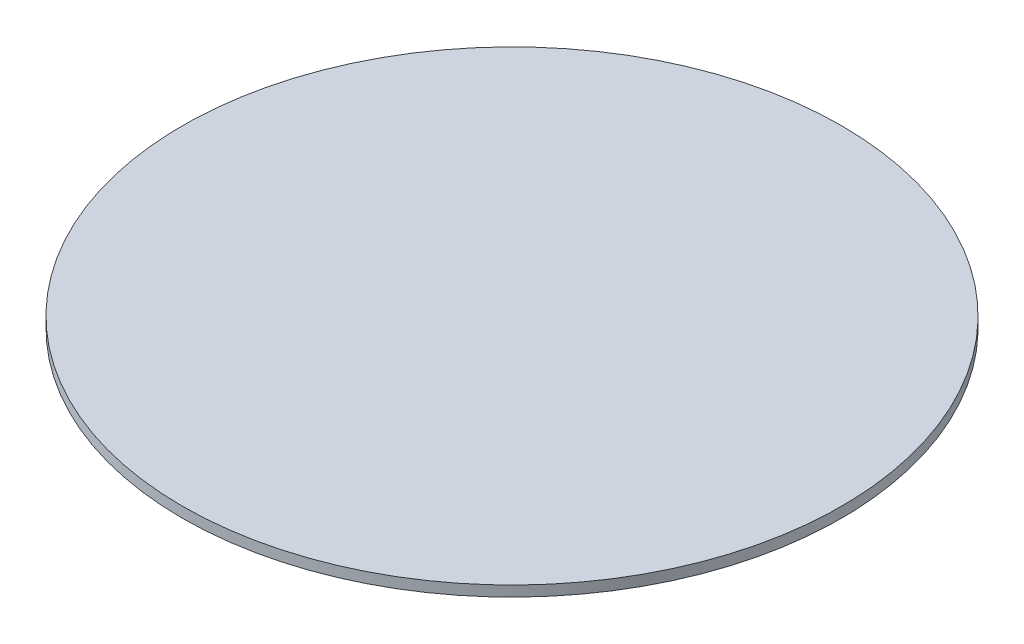
SolidWorks part; units mm, degrees
material "7075-T6 (SN)"
ref_plane "Front Plane" through (0, 0, 0) normal (0, 0, 1) x (1, 0, 0)
ref_plane "Top Plane" through (0, 0, 0) normal (0, 1, 0) x (1, 0, 0)
ref_plane "Right Plane" through (0, 0, 0) normal (1, 0, 0) x (0, 0, -1)
sketch "Sketch1" plane through (0, 0, 0) normal (0, 1, 0) x (1, 0, 0)
  circle A0 centre (0, 0) radius 1200
  dimension "D1" = 2400
extrude "Boss-Extrude1" add sketch "Sketch1" along normal blind 38.1
